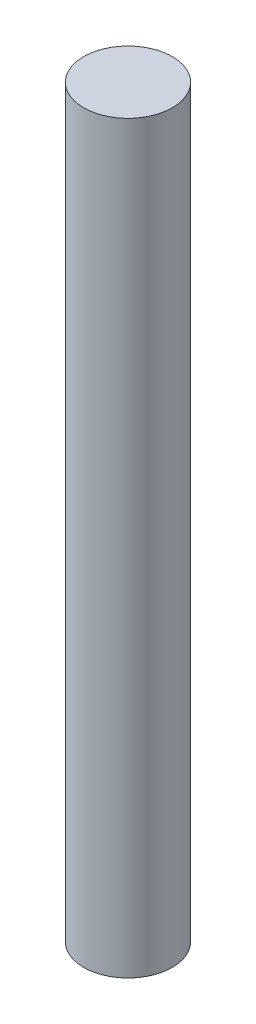
SolidWorks part; units mm, degrees
ref_plane "Front Plane" through (0, 0, 0) normal (0, 0, 1) x (1, 0, 0)
ref_plane "Top Plane" through (0, 0, 0) normal (0, 1, 0) x (1, 0, 0)
ref_plane "Right Plane" through (0, 0, 0) normal (1, 0, 0) x (0, 0, -1)
sketch "Sketch1" plane through (0, 0, 0) normal (0, 1, 0) x (1, 0, 0)
  circle A0 centre (0, 0) radius 2.5
  dimension "D1" = 5
extrude "Boss-Extrude1" add sketch "Sketch1" along normal blind 29 and the other way blind 13
